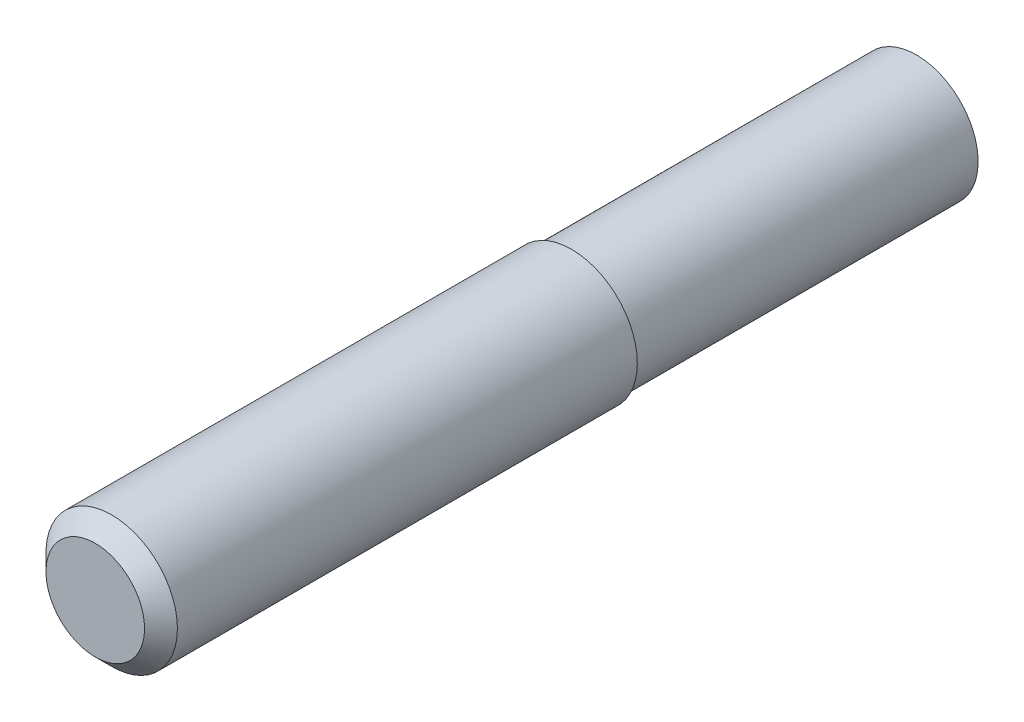
SolidWorks part; units mm, degrees
ref_plane "Ebene vorne" through (0, 0, 0) normal (0, 0, 1) x (1, 0, 0)
ref_plane "Ebene oben" through (0, 0, 0) normal (0, 1, 0) x (1, 0, 0)
ref_plane "Ebene rechts" through (0, 0, 0) normal (1, 0, 0) x (0, 0, -1)
sketch "Skizze1" plane through (0, 0, 0) normal (0, 0, 1) x (1, 0, 0)
  circle A0 centre (0, 0) radius 10
  dimension "D1" = 20
extrude "Aufsatz-Linear austragen1" add sketch "Skizze1" along normal blind 100
sketch "Skizze2" plane through (0, 0, 100) normal (0, 0, 1) x (1, 0, 0)
  circle A0 centre (0, 0) radius 8
  circle A1 centre (0, 0) radius 10
  dimension "D1" = 16
extrude "Schnitt-Linear austragen1" cut sketch "Skizze2" against normal blind 68
cosmetic thread "Gewindedarstellung1" parameters "D1"=15.5, "D2"=13.797
chamfer "Fase1" distance 2 angle 45 1 edges at (8, 0, 100)
sketch "Skizze3" plane through (0, 0, 0) normal (0, 0, -1) x (-1, 0, 0)
  circle A0 centre (0, 0) radius 7.5
  circle A1 centre (0, 0) radius 10
  dimension "D1" = 15
extrude "Schnitt-Linear austragen2" cut sketch "Skizze3" against normal blind 42
